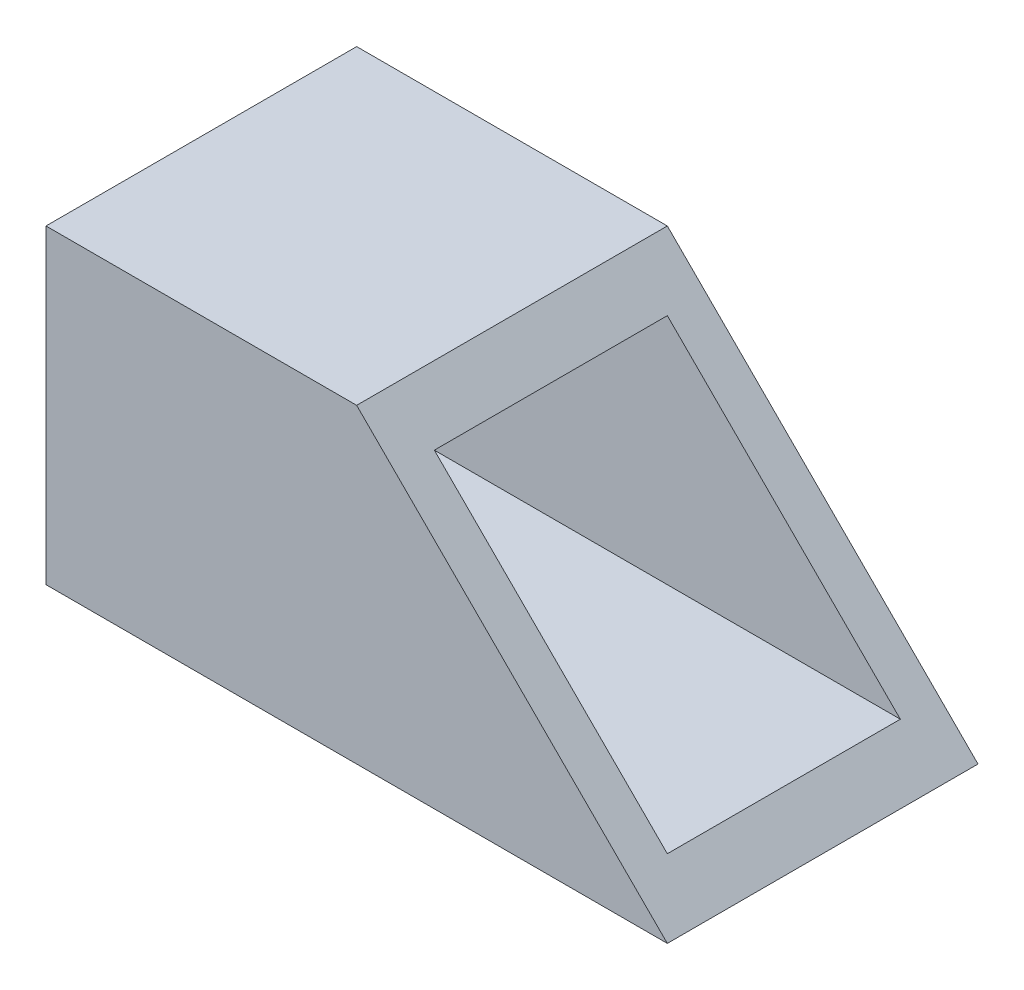
SolidWorks part; units mm, degrees
ref_plane "Front Plane" through (0, 0, 0) normal (0, 0, 1) x (1, 0, 0)
ref_plane "Top Plane" through (0, 0, 0) normal (0, 1, 0) x (1, 0, 0)
ref_plane "Right Plane" through (0, 0, 0) normal (1, 0, 0) x (0, 0, -1)
sketch "Sketch1" plane through (0, 0, 0) normal (1, 0, 0) x (0, 0, -1)
  line L1 (12.7, -12.7) -> (-12.7, -12.7)
  line L2 (12.7, -12.7) -> (12.7, 12.7)
  line L3 (12.7, 12.7) -> (-12.7, 12.7)
  line L4 (-12.7, -12.7) -> (-12.7, 12.7)
  line L5 (12.7, -12.7) -> (-12.7, 12.7) construction
  line L6 (12.7, 12.7) -> (-12.7, -12.7) construction
  line L7 (9.525, -9.525) -> (-9.525, -9.525)
  line L8 (9.525, -9.525) -> (9.525, 9.525)
  line L9 (9.525, 9.525) -> (-9.525, 9.525)
  line L10 (-9.525, -9.525) -> (-9.525, 9.525)
  line L11 (9.525, -9.525) -> (-9.525, 9.525) construction
  line L12 (9.525, 9.525) -> (-9.525, -9.525) construction
  point P0 (0, 0)
  point P6 (0, 0)
  dimension "D1" = 25.4
  dimension "D2" = 19.05
extrude "Boss-Extrude1" add sketch "Sketch1" along normal blind 50.8
sketch "Sketch2" plane through (0, 0, -12.7) normal (0, 0, -1) x (-1, 0, 0)
  line L0 (-50.8, -12.7) -> (-25.4, 12.7)
  line L1 (-50.8, 12.7) -> (0, 12.7) construction
  line L2 (-50.8, -12.7) -> (0, -12.7) construction
  line L3 (-50.8, -12.7) -> (-50.8, 12.7)
  line L4 (-50.8, 12.7) -> (-25.4, 12.7)
  dimension "D1" = 45
extrude "Cut-Extrude1" cut sketch "Sketch2" against normal through all
